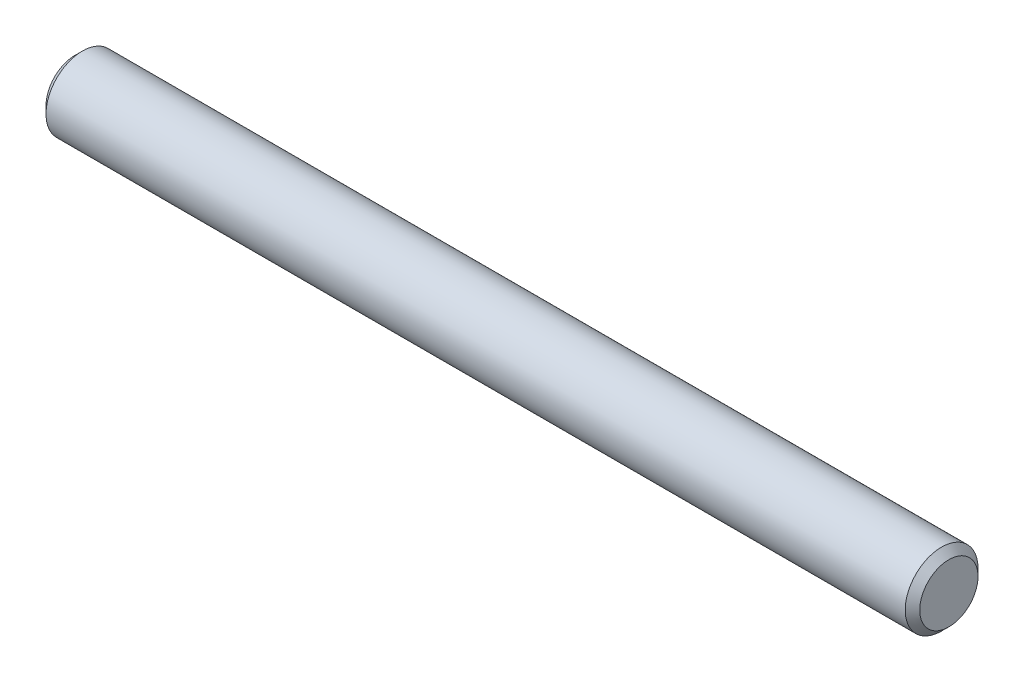
SolidWorks part; units mm, degrees
material "A-Glass Fiber"
ref_plane "Front" through (0, 0, 0) normal (0, 0, 1) x (1, 0, 0)
ref_plane "Top" through (0, 0, 0) normal (0, 1, 0) x (1, 0, 0)
ref_plane "Right" through (0, 0, 0) normal (1, 0, 0) x (0, 0, -1)
sketch "Sketch1" plane through (0, 0, 0) normal (0, 0, 1) x (1, 0, 0)
  line L0 (-9.525, 0) -> (9.525, 0) construction
  line L1 (9.525, 0.7937) -> (9.525, -0.7937) construction
  line L2 (-9.525, 0.7937) -> (-9.525, -0.7937) construction
  dimension "Length" = 19.05
  dimension "Diameter" = 1.5875
sketch "Sketch2" plane through (0, 0, 0) normal (1, 0, 0) x (0, 0, -1)
  circle A0 centre (0, 0) radius 0.7937
extrude "Extrude1" add sketch "Sketch2" against normal up to vertex (9.525 mm away) and the other way up to vertex (9.525 mm away) up to point (-9.525, 0.7937, 0) other way up to point (9.525, 0.7937, 0)
chamfer "Chamfer1" distance 0.1588 angle 45 2 edges at (9.525, 0, -0.7937) (-9.525, 0, -0.7937)
equation "\"D1@Chamfer1\" = \"Diameter@Sketch1\"*.1"
